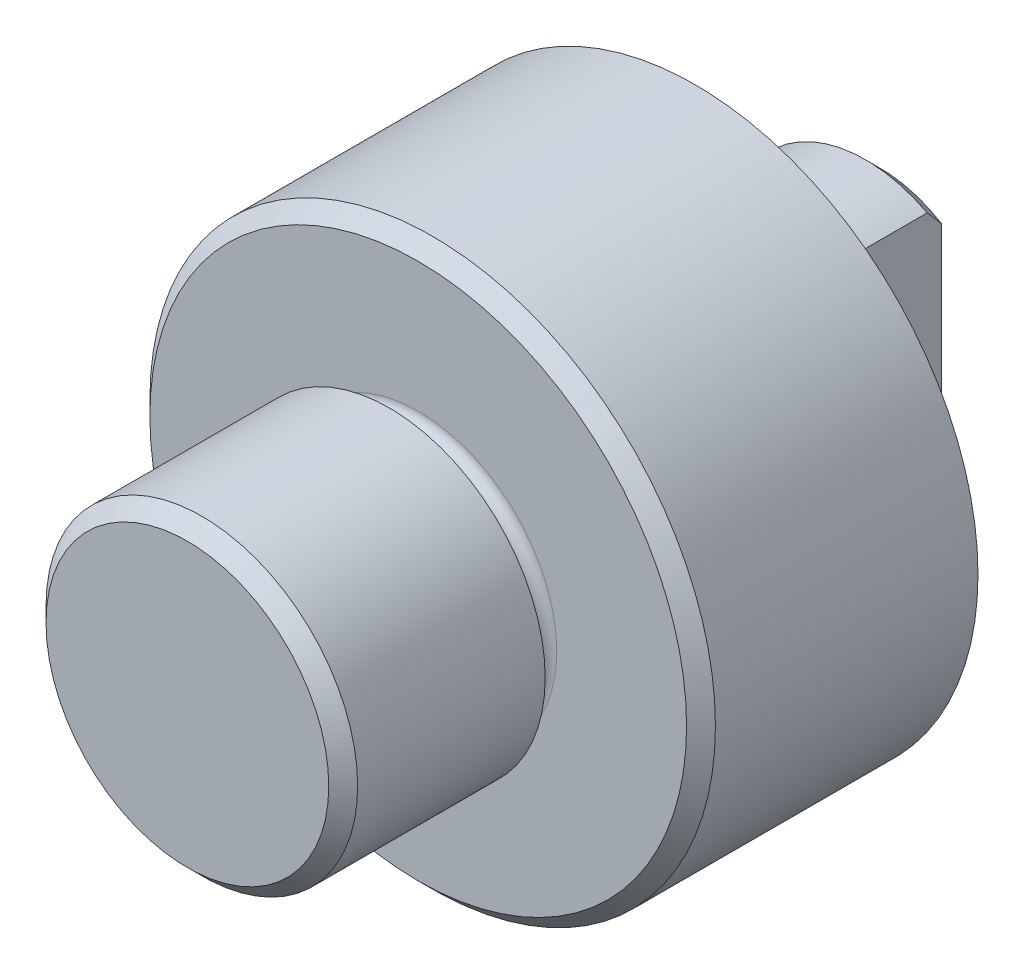
SolidWorks part; units mm, degrees
ref_plane "Front Plane" through (0, 0, 0) normal (0, 0, 1) x (1, 0, 0)
ref_plane "Top Plane" through (0, 0, 0) normal (0, 1, 0) x (1, 0, 0)
ref_plane "Right Plane" through (0, 0, 0) normal (1, 0, 0) x (0, 0, -1)
sketch "Sketch1" plane through (0, 0, 0) normal (1, 0, 0) x (0, 0, -1)
  line L0 (-127.0185, 0) -> (111.9377, 0) construction
  line L1 (-70, 0) -> (-70, 27)
  line L2 (-30, 22) -> (-35, 22)
  line L3 (-30, 22) -> (-30, 49)
  line L4 (-30, 49) -> (18, 49)
  line L5 (18, 49) -> (18, 23)
  line L6 (18, 23) -> (50, 23)
  line L7 (50, 23) -> (50, 0)
  line L8 (-70, 0) -> (50, 0)
  line L9 (-35, 22) -> (-35, 27)
  line L10 (-35, 27) -> (-70, 27)
  dimension "D1" = 27
  dimension "D2" = 49
  dimension "D3" = 32
  dimension "D4" = 48
  dimension "D5" = 120
  dimension "D6" = 23
  dimension "D7" = 5
  dimension "D8" = 18
revolve "Revolve1" add sketch "Sketch1" angle 360 about L0
chamfer "Chamfer1" distance 2.5 angle 45 3 edges at (23, 0, -50) (49, 0, 30) (27, 0, 70)
ref_plane "Plane1" through (0, -49, 0) normal (0, -1, 0) x (-1, 0, 0)
sketch "Sketch3" plane through (0, -49, 0) normal (0, -1, 0) x (-1, 0, 0)
  line L0 (0, -18) -> (0, 10) construction
  line L1 (-4, -18) -> (-4, 10)
  line L2 (4, -18) -> (4, 10)
  line L3 (49, 18) -> (-49, 18) construction
  arc A0 (-4, -18) -> (4, -18) centre (0, -18) ccw
  arc A1 (4, 10) -> (-4, 10) centre (0, 10) ccw
  point P2 (0, -4)
  dimension "D1" = 4
  dimension "D2" = 4
  dimension "D3" = 8
extrude "Cut-Extrude1" cut sketch "Sketch3" against normal blind 5.5
ref_plane "Plane2" through (10.7, 0, 0) normal (1, 0, 0) x (0, 0, -1)
sketch "Sketch5" plane through (10.7, 0, 0) normal (1, 0, 0) x (0, 0, -1)
  line L1 (18, 23) -> (54, 23)
  line L2 (18, 23) -> (18, -20)
  line L3 (18, -20) -> (54, -20)
  line L4 (54, 23) -> (54, -20)
  dimension "D1" = 36
  dimension "D2" = 20
extrude "Cut-Extrude2" cut sketch "Sketch5" along normal blind 12.3
sketch "Sketch6" plane through (10.7, 0, 0) normal (1, 0, 0) x (0, 0, -1)
  line L0 (18, 20.3595) -> (18, -20) construction
  circle A0 centre (33, 0) radius 6
  dimension "D1" = 15
  dimension "D2" = 12
extrude "Cut-Extrude3" cut sketch "Sketch6" against normal blind 8.4
ref_plane "Plane3" through (2.3, 0, 0) normal (1, 0, 0) x (0, 0, -1)
sketch "Sketch7" plane through (2.3, 0, 0) normal (1, 0, 0) x (0, 0, -1)
  circle A0 centre (33, 0) radius 6
  circle A2 centre (33, 0) radius 6 construction
sketch "Sketch8" plane through (0, 0, 0) normal (1, 0, 0) x (0, 0, -1)
  point P0 (33, 0)
loft "Cut-Loft1" cut profiles "Sketch8", "Sketch7"
fillet "Fillet2" radius 2 2 edges at (22, 0, 35) (22, 0, 30)
